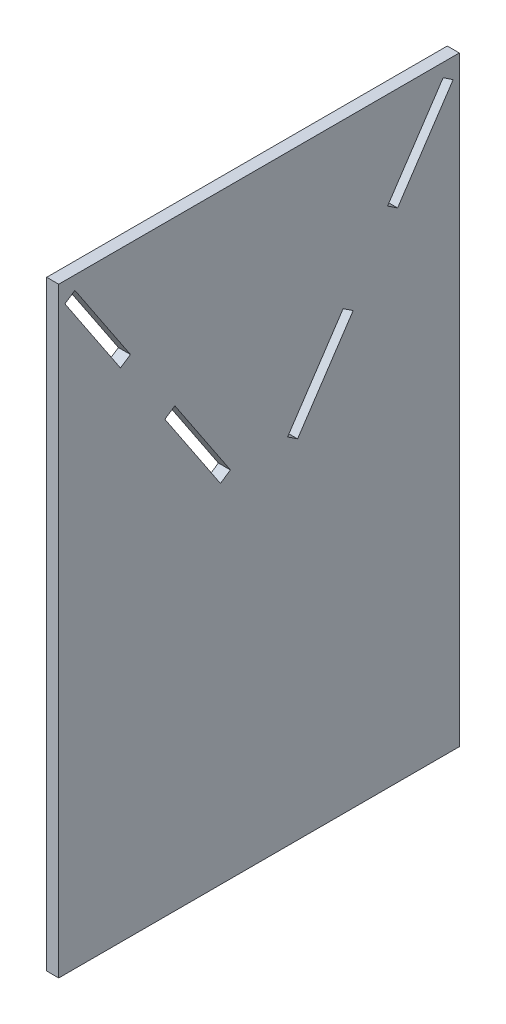
SolidWorks part; units mm, degrees
ref_plane "Спереди" through (0, 0, 0) normal (0, 0, 1) x (1, 0, 0)
ref_plane "Сверху" through (0, 0, 0) normal (0, 1, 0) x (1, 0, 0)
ref_plane "Справа" through (0, 0, 0) normal (1, 0, 0) x (0, 0, -1)
sketch "Эскиз1" plane through (0, 0, 0) normal (1, 0, 0) x (0, 0, -1)
  line L0 (0, 0) -> (0, 197.6692) construction
  line L1 (100, 150) -> (-100, 150)
  line L2 (100, 150) -> (100, -150)
  line L3 (100, -150) -> (-100, -150)
  line L4 (-100, 150) -> (-100, -150)
  line L5 (100, 150) -> (-100, -150) construction
  line L6 (100, -150) -> (-16.7705, 25.1557) construction
  line L7 (-91.9323, 143.3068) -> (-96.9246, 139.9786)
  line L8 (-91.9323, 143.3068) -> (-64.1973, 101.7043)
  line L9 (-44.5055, 66.7582) -> (-100, 150) construction
  line L10 (-64.1973, 101.7043) -> (-69.1896, 98.3761)
  line L11 (-100, 137.9284) -> (-32.0264, 183.2441) construction
  line L12 (-96.9246, 139.9786) -> (-69.1896, 98.3761)
  line L13 (-19.2666, 23.4916) -> (-14.2743, 26.8198)
  line L14 (-47.0016, 65.0941) -> (-42.0093, 68.4223)
  line L15 (-14.2743, 26.8198) -> (-42.0093, 68.4223)
  line L16 (-19.2666, 23.4916) -> (-47.0016, 65.0941)
  line L17 (47.0016, 65.0941) -> (4.8099, 93.2219) construction
  line L18 (-47.0016, 65.0941) -> (-4.8099, 93.2219) construction
  line L19 (100, 137.9284) -> (32.0264, 183.2441) construction
  line L20 (44.5055, 66.7582) -> (100, 150) construction
  line L21 (-100, -150) -> (16.7705, 25.1557) construction
  line L22 (19.2666, 23.4916) -> (47.0016, 65.0941)
  line L23 (14.2743, 26.8198) -> (42.0093, 68.4223)
  line L24 (47.0016, 65.0941) -> (42.0093, 68.4223)
  line L25 (19.2666, 23.4916) -> (14.2743, 26.8198)
  line L26 (96.9246, 139.9786) -> (69.1896, 98.3761)
  line L27 (64.1973, 101.7043) -> (69.1896, 98.3761)
  line L28 (91.9323, 143.3068) -> (64.1973, 101.7043)
  line L29 (91.9323, 143.3068) -> (96.9246, 139.9786)
  line L30 (94.4285, 141.6427) -> (100, 150) construction
  line L31 (-42.0093, 68.4223) -> (62.4775, 68.4223) construction
  line L32 (-64.1973, 101.7043) -> (64.1973, 101.7043) construction
  point P0 (0, 0)
  point P12 (-32.0264, 48.0396)
  point P35 (32.0264, 48.0396)
  dimension "D1" = 300
  dimension "D2" = 200
  dimension "D3" = 50
  dimension "D4" = 50
  dimension "D5" = 6
  dimension "D6" = 50
  dimension "D7" = 6
  dimension "D8" = 6
extrude "Бобышка-Вытянуть1" add sketch "Эскиз1" along normal blind 6
